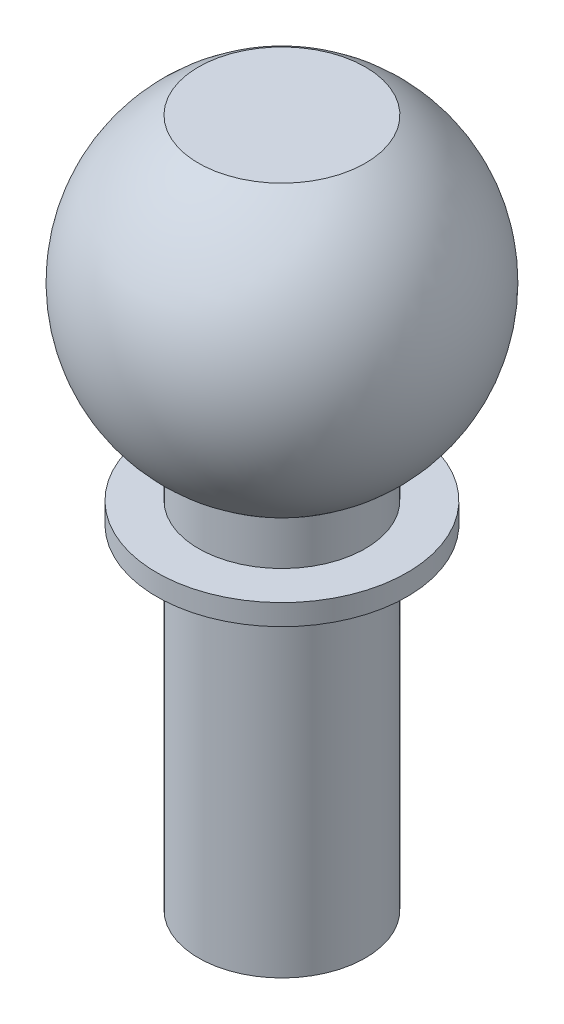
SolidWorks part; units mm, degrees
material "Chrome Stainless Steel"
ref_plane "Front Plane" through (0, 0, 0) normal (0, 0, 1) x (1, 0, 0)
ref_plane "Top Plane" through (0, 0, 0) normal (0, 1, 0) x (1, 0, 0)
ref_plane "Right Plane" through (0, 0, 0) normal (1, 0, 0) x (0, 0, -1)
sketch "Sketch1" plane through (0, 0, 0) normal (0, 0, 1) x (1, 0, 0)
  line L0 (0, 0) -> (20, 0)
  line L1 (20, 0) -> (20, 80)
  line L2 (20, 80) -> (30, 80)
  line L3 (30, 80) -> (30, 85)
  line L4 (30, 85) -> (20, 85)
  line L5 (20, 85) -> (20, 95.718)
  line L6 (0, 0) -> (0, 165)
  line L7 (0, 165) -> (20, 165)
  arc A0 (20, 95.718) -> (20, 165) centre (0, 130.359) ccw
  dimension "D5" = 40
  dimension "D1" = 20
  dimension "D2" = 80
  dimension "D3" = 30
  dimension "D4" = 5
  dimension "D6" = 85
revolve "Revolve1" add sketch "Sketch1" angle 360 about L6
